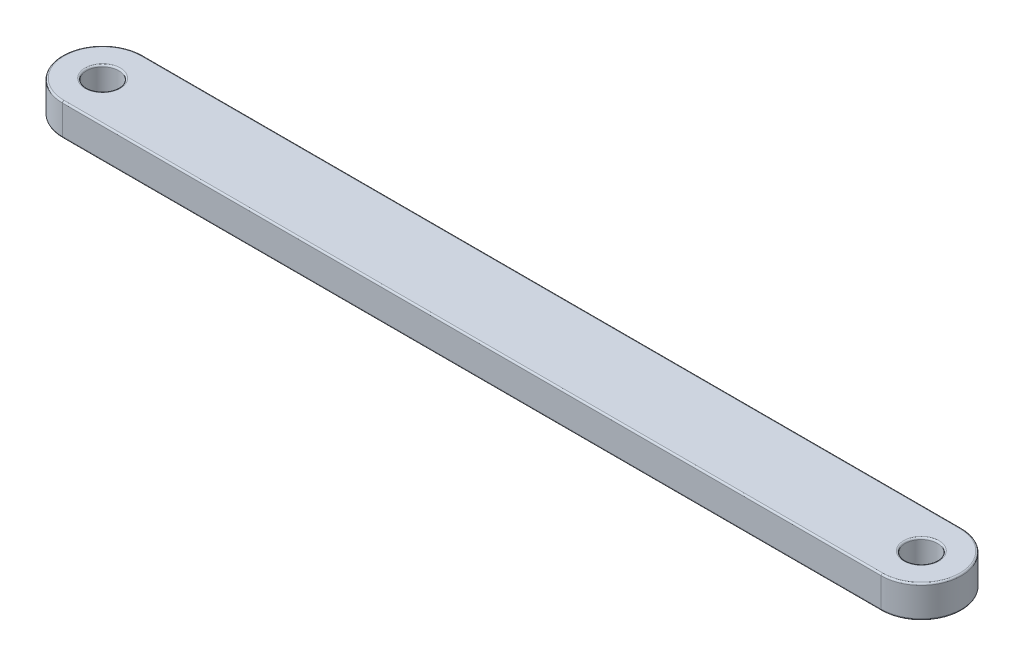
SolidWorks part; units mm, degrees
material "Alloy Steel"
ref_plane "Front Plane" through (0, 0, 0) normal (0, 0, 1) x (1, 0, 0)
ref_plane "Top Plane" through (0, 0, 0) normal (0, 1, 0) x (1, 0, 0)
ref_plane "Right Plane" through (0, 0, 0) normal (1, 0, 0) x (0, 0, -1)
sketch "Sketch1" plane through (0, 0, 0) normal (0, 1, 0) x (1, 0, 0)
  line L0 (-255, 0) -> (255, 0) construction
  line L1 (-255, 25) -> (255, 25)
  line L2 (-255, -25) -> (255, -25)
  line L3 (0, 0) -> (0, 241.5958) construction
  arc A0 (-255, 25) -> (-255, -25) centre (-255, 0) ccw
  arc A1 (255, -25) -> (255, 25) centre (255, 0) ccw
  circle A2 centre (-255, 0) radius 10
  circle A3 centre (255, 0) radius 10
  point P2 (0, 0)
  dimension "D2" = 20
  dimension "D3" = 50
  dimension "D1" = 510
extrude "Boss-Extrude1" add sketch "Sketch1" along normal blind 20
fillet "Fillet1" radius 1 12 edges at (255, 0, -10) (-255, 0, 10) (0, 0, 25) (280, 0, 0) (0, 0, -25) (-280, 0, 0) (255, 20, -10) (0, 20, -25) (280, 20, 0) (0, 20, 25) (-280, 20, 0) (-255, 20, 10)
